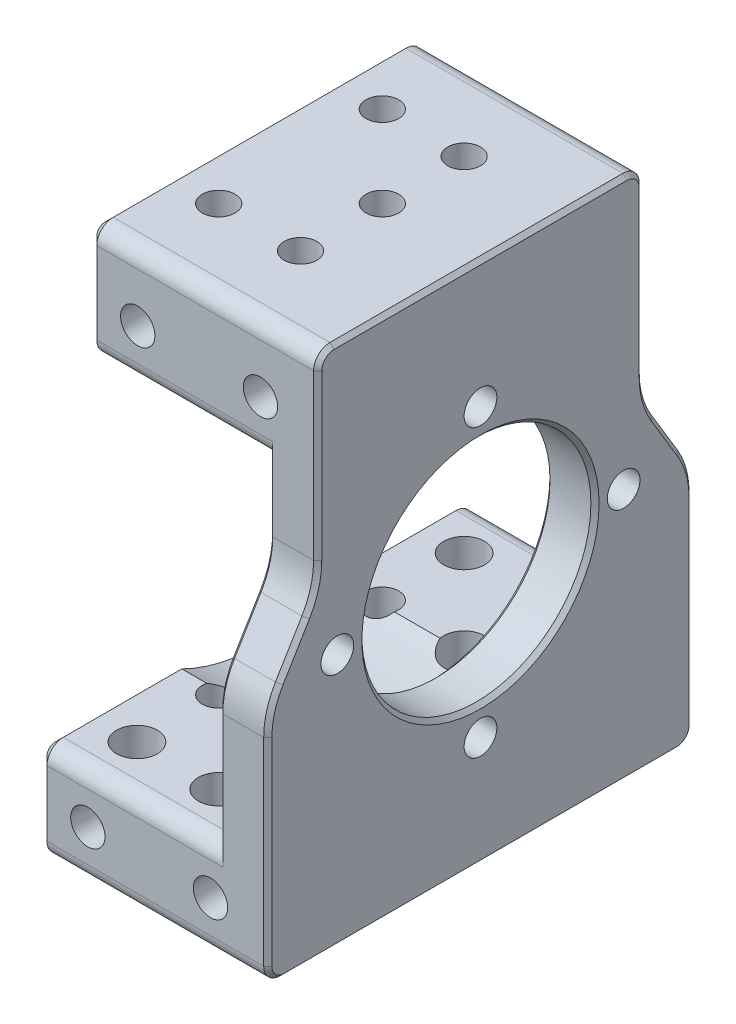
SolidWorks part; units mm, degrees
ref_plane "前视基准面" through (0, 0, 0) normal (0, 0, 1) x (1, 0, 0)
ref_plane "上视基准面" through (0, 0, 0) normal (0, 1, 0) x (1, 0, 0)
ref_plane "右视基准面" through (0, 0, 0) normal (1, 0, 0) x (0, 0, -1)
ref_plane "基准面4" through (7.5583, 0, 0) normal (1, 0, 0) x (0, 0, -1)
sketch "草图1" plane through (7.5583, 0, 0) normal (1, 0, 0) x (0, 0, -1)
  line L0 (0, 54.2822) -> (-52, 54.2822)
  line L1 (-52, 54.2822) -> (-52, -9.7178)
  line L2 (-52, -9.7178) -> (0, -9.7178)
  line L3 (0, -9.7178) -> (0, 54.2822)
extrude "凸台-拉伸1" add sketch "草图1" against normal blind 28
sketch "草图2" plane through (0, 0, 0) normal (0, 0, -1) x (-1, 0, 0)
  line L0 (20.4417, 54.2822) -> (-1.5583, 54.2822)
  line L1 (-1.5583, 54.2822) -> (-1.5583, 2.2822)
  line L2 (-1.5583, 2.2822) -> (20.4417, 2.2822)
  line L3 (20.4417, 2.2822) -> (20.4417, 54.2822)
extrude "切除-拉伸1" cut sketch "草图2" against normal through all
sketch "草图3" plane through (7.5583, 0, 0) normal (1, 0, 0) x (0, 0, -1)
  line L0 (-52, 19.2822) -> (-45.9, 19.2822)
  line L1 (-45.9, 19.2822) -> (-45.9, 54.2822)
  line L2 (-45.9, 54.2822) -> (-52, 54.2822)
  line L3 (-52, 54.2822) -> (-52, 19.2822)
extrude "切除-拉伸2" cut sketch "草图3" against normal through all
sketch "草图4" plane through (7.5583, 0, 0) normal (1, 0, 0) x (0, 0, -1)
  line L0 (-6.1, 54.2822) -> (-6.1, 19.2822)
  line L1 (-6.1, 19.2822) -> (0, 19.2822)
  line L2 (0, 19.2822) -> (0, 54.2822)
  line L3 (0, 54.2822) -> (-6.1, 54.2822)
extrude "切除-拉伸3" cut sketch "草图4" against normal through all
sketch "草图5" plane through (1.5583, 0, 0) normal (-1, 0, 0) x (0, 0, 1)
  line L0 (6.1, 54.2822) -> (45.9, 54.2822)
  line L1 (45.9, 54.2822) -> (45.9, 40.2822)
  line L2 (45.9, 40.2822) -> (6.1, 40.2822)
  line L3 (6.1, 40.2822) -> (6.1, 54.2822)
extrude "凸台-拉伸2" add sketch "草图5" along normal blind 22
sketch "草图6" plane through (-20.4417, 0, 0) normal (-1, 0, 0) x (0, 0, 1)
  line L0 (16.4836, 40.2822) -> (35.5164, 40.2822)
  arc A0 (35.5164, 40.2822) -> (16.4836, 40.2822) centre (26, 21.2822) ccw
extrude "切除-拉伸4" cut sketch "草图6" against normal blind 22
sketch "草图7" plane through (-20.4417, 0, 0) normal (-1, 0, 0) x (0, 0, 1)
  line L0 (35.5164, 2.2822) -> (16.4836, 2.2822)
  arc A0 (16.4836, 2.2822) -> (35.5164, 2.2822) centre (26, 21.2822) ccw
extrude "切除-拉伸5" cut sketch "草图7" against normal blind 22
draft "拔模1" type of draft neutral plane draft angle 58.967 faces to draft 1 face at (4.5583, 19.2822, 48.95) neutral plane through (-20.4417, 54.2822, 52) neutral plane normal (0, 0, 1) parameters "D1"=58.967
draft "拔模2" type of draft neutral plane draft angle 58.967 faces to draft 1 face at (4.5583, 19.2822, 3.05) neutral plane through (-20.4417, -9.7178, 0) neutral plane normal (0, 0, -1) parameters "D1"=58.967
hole_wizard "Ø5.0 (5) 直径孔1" positions "草图9" profile "草图8" hole size "Ø5.0" standard "ANSI Metric"
sketch "草图9" plane through (0, -9.7178, 0) normal (0, -1, 0) x (-1, 0, 0)
  point P0 (4.4417, -26)
sketch "草图8" plane through (-4.4417, -9.7178, 26) normal (1, 0, 0) x (0, 0, -1)
  line L0 (0, 0) -> (0, 9.75)
  line L1 (0, 9.75) -> (2.5, 9.75)
  line L2 (2.5, 9.75) -> (2.5, 0)
  line L5 (2.5, 0) -> (0, 0)
  line L11 (0, -6.35) -> (0, 107.95) construction
  dimension "通孔孔直径" = 5
  dimension "通孔孔深度" = 9.75
hole_wizard "Ø5.0 (5) 直径孔2" positions "草图11" profile "草图10" hole size "Ø5.0" standard "ANSI Metric"
sketch "草图11" plane through (0, -9.7178, 0) normal (0, -1, 0) x (-1, 0, 0)
  point P0 (4.4417, -36)
  point P1 (4.4417, -16)
sketch "草图10" plane through (-4.4417, -9.7178, 36) normal (1, 0, 0) x (0, 0, -1)
  line L0 (0, 0) -> (0, 12)
  line L1 (0, 12) -> (2.5, 12)
  line L2 (2.5, 12) -> (2.5, 0)
  line L5 (2.5, 0) -> (0, 0)
  line L11 (0, -6.35) -> (0, 107.95) construction
  dimension "通孔孔直径" = 5
  dimension "通孔孔深度" = 12
hole_wizard "Ø4.0 (4) 直径孔2" positions "草图13" profile "草图12" hole size "Ø4.0" standard "ANSI Metric" end condition through all
sketch "草图13" plane through (0, 54.2822, 0) normal (0, 1, 0) x (1, 0, 0)
  point P0 (-4.4417, -26)
sketch "草图12" plane through (-4.4417, 54.2822, 26) normal (1, 0, 0) x (0, 0, 1)
  line L0 (0, 0) -> (0, 64)
  line L1 (0, 64) -> (2, 64)
  line L2 (2, 64) -> (2, 0)
  line L5 (2, 0) -> (0, 0)
  line L11 (0, -6.35) -> (0, 107.95) construction
  dimension "通孔孔直径" = 4
  dimension "通孔孔深度" = 64
hole_wizard "Ø4.0 (4) 直径孔3" positions "草图15" profile "草图14" hole size "Ø4.0" standard "ANSI Metric" end condition through all
sketch "草图15" plane through (0, 54.2822, 0) normal (0, 1, 0) x (1, 0, 0)
  point P0 (-4.4417, -36)
  point P1 (-4.4417, -16)
sketch "草图14" plane through (-4.4417, 54.2822, 36) normal (1, 0, 0) x (0, 0, 1)
  line L0 (0, 0) -> (0, 64)
  line L1 (0, 64) -> (2, 64)
  line L2 (2, 64) -> (2, 0)
  line L5 (2, 0) -> (0, 0)
  line L11 (0, -6.35) -> (0, 107.95) construction
  dimension "通孔孔直径" = 4
  dimension "通孔孔深度" = 64
hole_wizard "M24 间隙孔1" positions "草图17" profile "草图16" hole size "M24" standard "ANSI Metric"
sketch "草图17" plane through (7.5583, 0, 0) normal (1, 0, 0) x (0, 0, -1)
  point P0 (-26, 21.2822)
sketch "草图16" plane through (7.5583, 21.2822, 26) normal (0, 1, 0) x (0, 0, -1)
  line L0 (0, 0) -> (0, 28)
  line L1 (0, 28) -> (14, 28)
  line L2 (14, 28) -> (14, 0)
  line L5 (14, 0) -> (0, 0)
  line L11 (0, -6.35) -> (0, 107.95) construction
  dimension "通孔孔直径" = 28
  dimension "通孔孔深度" = 28
hole_wizard "Ø4.0 (4) 直径孔1" positions "草图19" profile "草图18" hole size "Ø4.0" standard "ANSI Metric"
sketch "草图19" plane through (1.5583, 0, 0) normal (-1, 0, 0) x (0, 0, 1)
  point P0 (43.5, 21.2822)
  point P1 (8.5, 21.2822)
  point P2 (26, 3.7822)
  point P3 (26, 38.7822)
sketch "草图18" plane through (1.5583, 21.2822, 43.5) normal (0, 1, 0) x (0, 0, 1)
  line L0 (0, 0) -> (0, 6)
  line L1 (0, 6) -> (2, 6)
  line L2 (2, 6) -> (2, 0)
  line L5 (2, 0) -> (0, 0)
  line L11 (0, -6.35) -> (0, 107.95) construction
  dimension "通孔孔直径" = 4
  dimension "通孔孔深度" = 6
hole_wizard "Ø4.2 (4.2) 直径孔1" positions "草图21" profile "草图20" hole size "Ø4.2" standard "ANSI Metric"
sketch "草图21" plane through (0, 0, 52) normal (0, 0, 1) x (1, 0, 0)
  point P0 (0.5583, -3.7178)
sketch "草图20" plane through (0.5583, -3.7178, 52) normal (1, 0, 0) x (0, -1, 0)
  line L0 (0, 0) -> (0, 52)
  line L1 (0, 52) -> (2.1, 52)
  line L2 (2.1, 52) -> (2.1, 0)
  line L5 (2.1, 0) -> (0, 0)
  line L11 (0, -6.35) -> (0, 107.95) construction
  dimension "通孔孔直径" = 4.2
  dimension "通孔孔深度" = 52
hole_wizard "Ø5.0 (5) 直径孔3" positions "草图23" profile "草图22" hole size "Ø5.0" standard "ANSI Metric"
sketch "草图23" plane through (0, 2.2822, 0) normal (0, 1, 0) x (1, 0, 0)
  point P0 (-4.4417, -46)
  point P1 (-4.4417, -6)
sketch "草图22" plane through (-4.4417, 2.2822, 46) normal (1, 0, 0) x (0, 0, 1)
  line L0 (0, 0) -> (0, 12)
  line L1 (0, 12) -> (2.5, 12)
  line L2 (2.5, 12) -> (2.5, 0)
  line L5 (2.5, 0) -> (0, 0)
  line L11 (0, -6.35) -> (0, 107.95) construction
  dimension "通孔孔直径" = 5
  dimension "通孔孔深度" = 12
hole_wizard "Ø4.2 (4.2) 直径孔2" positions "草图25" profile "草图24" hole size "Ø4.2" standard "ANSI Metric"
sketch "草图25" plane through (0, 0, 0) normal (0, 0, -1) x (-1, 0, 0)
  point P0 (14.4417, -3.7178)
sketch "草图24" plane through (-14.4417, -3.7178, 0) normal (1, 0, 0) x (0, 1, 0)
  line L0 (0, 0) -> (0, 52)
  line L1 (0, 52) -> (2.1, 52)
  line L2 (2.1, 52) -> (2.1, 0)
  line L5 (2.1, 0) -> (0, 0)
  line L11 (0, -6.35) -> (0, 107.95) construction
  dimension "通孔孔直径" = 4.2
  dimension "通孔孔深度" = 52
ref_plane "基准面5" through (0, 0.0963, 0) normal (0, 1, 0) x (1, 0, 0)
hole_wizard "Ø5.0 (5) 直径孔4" positions "草图27" profile "草图26" hole size "Ø5.0" standard "ANSI Metric"
sketch "草图27" plane through (0, 0.0963, 0) normal (0, 1, 0) x (1, 0, 0)
  point P0 (-14.4417, -26)
sketch "草图26" plane through (-14.4417, 0.0963, 26) normal (1, 0, 0) x (0, 0, 1)
  line L0 (0, 0) -> (0, 9.8142)
  line L1 (0, 9.8142) -> (2.5, 9.8142)
  line L2 (2.5, 9.8142) -> (2.5, 0)
  line L5 (2.5, 0) -> (0, 0)
  line L11 (0, -6.35) -> (0, 107.95) construction
  dimension "通孔孔直径" = 5
  dimension "通孔孔深度" = 9.8142
ref_plane "基准面6" through (0, -2.4188, 0) normal (0, -1, 0) x (-1, 0, 0)
hole_wizard "Ø4.0 (4) 直径孔4" positions "草图29" profile "草图28" hole size "Ø4.0" standard "ANSI Metric"
sketch "草图29" plane through (0, -2.4188, 0) normal (0, -1, 0) x (-1, 0, 0)
  point P0 (14.4417, -36)
  point P1 (14.4417, -16)
sketch "草图28" plane through (-14.4417, -2.4188, 36) normal (1, 0, 0) x (0, 0, -1)
  line L0 (0, 0) -> (0, 85.3)
  line L1 (0, 85.3) -> (2, 85.3)
  line L2 (2, 85.3) -> (2, 0)
  line L5 (2, 0) -> (0, 0)
  line L10 (0, 85.3) -> (-2, 85.3) construction
  line L11 (0, -6.35) -> (0, 107.95) construction
  dimension "孔直径" = 4
  dimension "孔深度" = 85.3
  dimension "导头角度" = 180
hole_wizard "Ø5.0 (5) 直径孔6" positions "草图31" profile "草图30" hole size "Ø5.0" standard "ANSI Metric"
sketch "草图31" plane through (0, 2.2822, 0) normal (0, 1, 0) x (1, 0, 0)
  point P0 (-14.4417, -46)
  point P1 (-14.4417, -6)
sketch "草图30" plane through (-14.4417, 2.2822, 46) normal (1, 0, 0) x (0, 0, 1)
  line L0 (0, 0) -> (0, 16.7)
  line L1 (0, 16.7) -> (2.5, 16.7)
  line L2 (2.5, 16.7) -> (2.5, 0)
  line L5 (2.5, 0) -> (0, 0)
  line L10 (0, 16.7) -> (-2.5, 16.7) construction
  line L11 (0, -6.35) -> (0, 107.95) construction
  dimension "孔直径" = 5
  dimension "孔深度" = 16.7
  dimension "导头角度" = 180
hole_wizard "Ø4.2 (4.2) 直径孔3" positions "草图33" profile "草图32" hole size "Ø4.2" standard "ANSI Metric"
sketch "草图33" plane through (0, 0, 6.1) normal (0, 0, -1) x (-1, 0, 0)
  point P0 (14.4417, 46.2822)
  point P1 (-0.5583, 46.2822)
sketch "草图32" plane through (-14.4417, 46.2822, 6.1) normal (1, 0, 0) x (0, 1, 0)
  line L0 (0, 0) -> (0, 45.9)
  line L1 (0, 45.9) -> (2.1, 45.9)
  line L2 (2.1, 45.9) -> (2.1, 0)
  line L5 (2.1, 0) -> (0, 0)
  line L11 (0, -6.35) -> (0, 107.95) construction
  dimension "通孔孔直径" = 4.2
  dimension "通孔孔深度" = 45.9
fillet "圆角1" radius 2 8 edges at (-6.4417, 54.2822, 6.1) (-6.4417, -9.7178, 0) (-6.4417, -9.7178, 52) (-9.4417, 40.2822, 6.1) (-9.4417, 2.2822, 0) (-9.4417, 40.2822, 45.9) (-9.4417, 2.2822, 52) (-6.4417, 54.2822, 45.9)
fillet "圆角2" radius 10 4 edges at (4.5583, 19.2822, 0) (4.5583, 29.421, 45.9) (4.5583, 19.2822, 52) (4.5583, 29.421, 6.1)
chamfer "倒角1" distance 0.5 angle 45 28 edges at (1.5583, 8.394, 0) (1.5583, 19.181, 0.3645) (1.5583, 24.3516, 3.05) (1.5583, 29.5222, 5.7355) (1.5583, 37.2398, 6.1) (7.5583, 53.6964, 45.3142) (7.5583, 54.2822, 26) (7.5583, 42.2398, 45.9) (7.5583, 53.6964, 6.6858) (7.5583, 29.5222, 46.2645) (7.5583, 42.2398, 6.1) (7.5583, 24.3516, 48.95) (7.5583, 29.5222, 5.7355) (7.5583, 19.181, 51.6355) (7.5583, 24.3516, 3.05) (7.5583, 4.394, 52) (7.5583, 19.181, 0.3645) (7.5583, -9.132, 51.4142) (7.5583, 4.394, 0) (7.5583, -9.7178, 26) (7.5583, -9.132, 0.5858) (1.5583, 8.394, 52) (1.5583, 19.181, 51.6355) (1.5583, 24.3516, 48.95) (1.5583, 37.2398, 45.9) (1.5583, 29.5222, 46.2645) (1.5583, 21.2822, 12) (7.5583, 21.2822, 12)
chamfer "倒角2" distance 1 angle 45 20 edges at (-20.4417, 42.5322, 26) (-20.4417, 40.2822, 39.7082) (-20.4417, 40.2822, 12.2918) (-20.4417, 40.868, 45.3142) (-20.4417, 40.868, 6.6858) (-20.4417, 47.2822, 45.9) (-20.4417, 47.2822, 6.1) (-20.4417, 53.6964, 45.3142) (-20.4417, 53.6964, 6.6858) (-20.4417, 54.2822, 26) (-20.4417, -3.7178, 52) (-20.4417, -9.132, 51.4142) (-20.4417, 1.6964, 51.4142) (-20.4417, -9.7178, 26) (-20.4417, 2.2822, 42.7582) (-20.4417, -9.132, 0.5858) (-20.4417, 0.0322, 26) (-20.4417, -3.7178, 0) (-20.4417, 2.2822, 9.2418) (-20.4417, 1.6964, 0.5858)
sketch "草图34" plane through (0, -9.7178, 0) normal (0, -1, 0) x (1, 0, 0)
  circle A0 centre (-14.4417, 26) radius 2.5
extrude "切除-拉伸6" cut sketch "草图34" against normal blind 10
